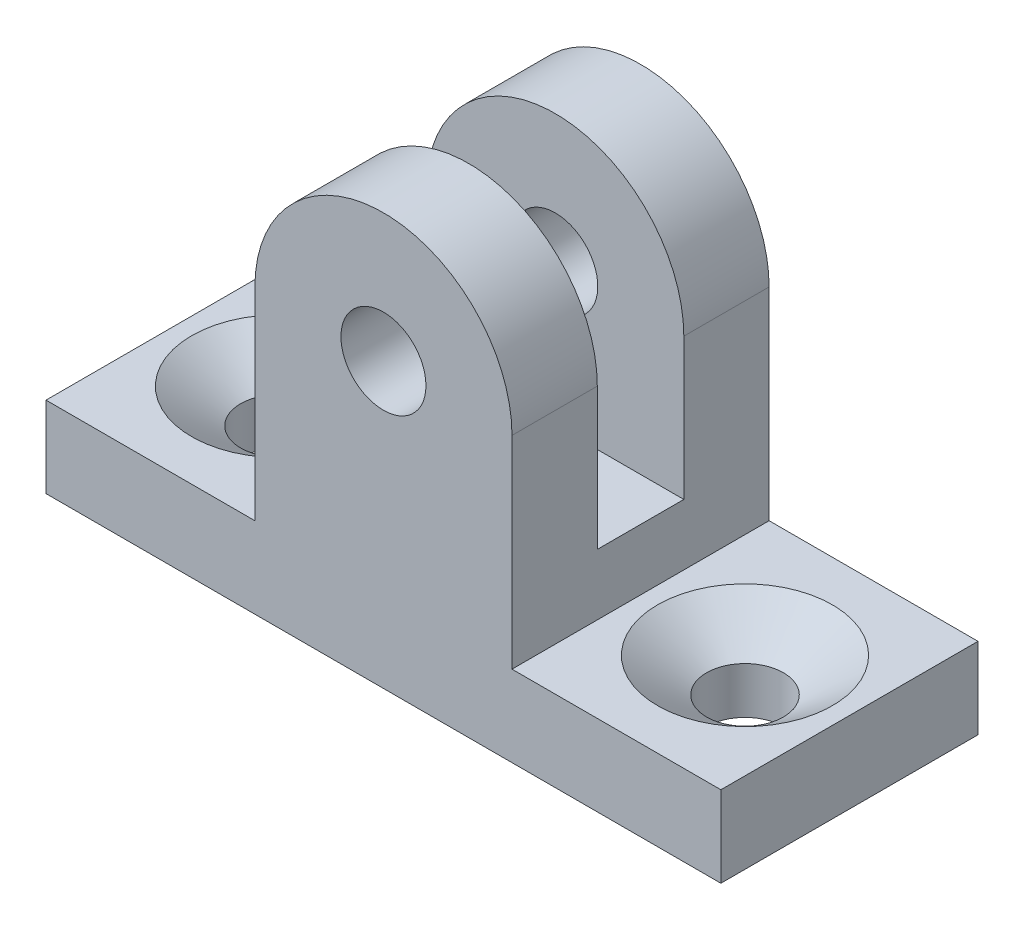
SolidWorks part; units mm, degrees
ref_plane "Front Plane" through (0, 0, 0) normal (0, 0, 1) x (1, 0, 0)
ref_plane "Top Plane" through (0, 0, 0) normal (0, 1, 0) x (1, 0, 0)
ref_plane "Right Plane" through (0, 0, 0) normal (1, 0, 0) x (0, 0, -1)
sketch "Sketch1" plane through (0, 0, 0) normal (0, 0, 1) x (1, 0, 0)
  line L0 (4.7625, 10.5) -> (4.7625, 3)
  line L1 (4.7625, 3) -> (12.5, 3)
  line L2 (12.5, 3) -> (12.5, 0)
  line L3 (-12.5, 3) -> (-12.5, 0)
  line L4 (4.7625, 10.5) -> (-4.7625, 10.5) construction
  line L5 (0, 10.5) -> (0, 0) construction
  line L6 (-12.5, 0) -> (12.5, 0)
  line L7 (-4.7625, 3) -> (-12.5, 3)
  line L8 (-4.7625, 10.5) -> (-4.7625, 3)
  arc A0 (-4.7625, 10.5) -> (4.7625, 10.5) centre (0, 10.5) cw
  circle A1 centre (0, 10.5) radius 1.575
  dimension "D1" = 7.5
  dimension "D2" = 4.7625
  dimension "D3" = 3
extrude "Boss-Extrude1" add sketch "Sketch1" along normal blind 9.525
sketch "Sketch2" plane through (-4.7625, 0, 0) normal (-1, 0, 0) x (0, 0, 1)
  line L0 (0, 0) -> (9.525, 0) construction
  line L1 (6.365, 15.2625) -> (6.365, 5.2625)
  line L2 (9.525, 15.2625) -> (0, 15.2625) construction
  line L3 (6.365, 5.2625) -> (3.16, 5.2625)
  line L4 (3.16, 5.2625) -> (3.16, 15.2625)
  line L5 (3.16, 15.2625) -> (6.365, 15.2625)
  line L6 (9.525, 10.5) -> (9.525, 15.2625) construction
  line L7 (0, 15.2625) -> (0, 10.5) construction
  dimension "D1" = 3.16
  dimension "D2" = 3.16
  dimension "D3" = 10
extrude "Cut-Extrude4" cut sketch "Sketch2" against normal up to surface (9.525 mm away) up to face at (4.7625, 6.75, 4.7625)
sketch "Sketch4" plane through (0, 3, 0) normal (0, 1, 0) x (1, 0, 0)
  line L0 (8.6313, 0) -> (8.6313, -9.525) construction
  line L1 (12.5, 0) -> (4.7625, 0) construction
  line L2 (12.5, -9.525) -> (4.7625, -9.525) construction
  line L3 (0, 0) -> (0, -9.525) construction
  line L4 (-4.7625, -9.525) -> (4.7625, -9.525) construction
  circle A0 centre (8.6313, -4.7625) radius 1.4224
  circle A1 centre (-8.6313, -4.7625) radius 1.4224
extrude "Cut-Extrude5" cut sketch "Sketch4" against normal up to surface (3 mm away) up to face at (0, 0, 4.7625)
sketch "Sketch5" plane through (0, 3, 0) normal (0, 1, 0) x (1, 0, 0)
  circle A0 centre (8.6313, -4.7625) radius 3.2385
  circle A1 centre (-8.6313, -4.7625) radius 3.2385
  dimension "D1" = 6.477
extrude "Cut-Extrude6" cut sketch "Sketch5" against normal blind 2.2 draft 55 contours A0 | A1
